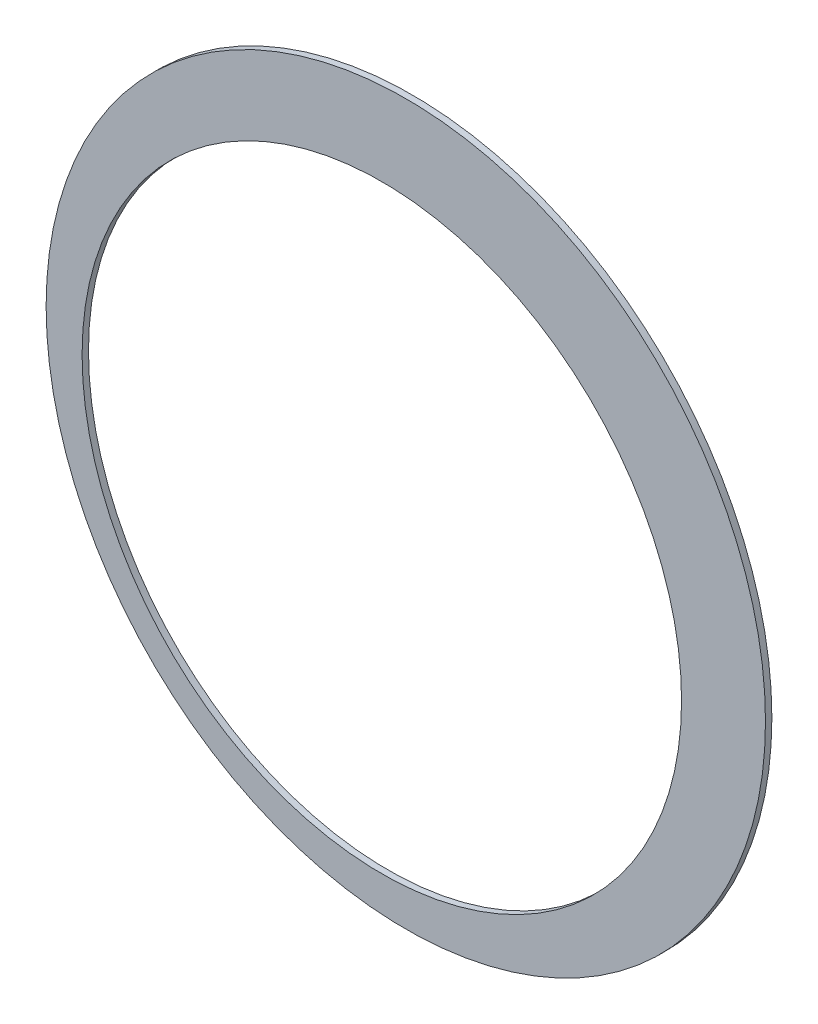
SolidWorks part; units mm, degrees
ref_plane "Front" through (0, 0, 0) normal (0, 0, 1) x (1, 0, 0)
ref_plane "Top" through (0, 0, 0) normal (0, 1, 0) x (1, 0, 0)
ref_plane "Right" through (0, 0, 0) normal (1, 0, 0) x (0, 0, -1)
sketch "Sketch1" plane through (0, 0, 0) normal (0, 0, 1) x (1, 0, 0)
  circle A0 centre (0, 0) radius 37.5
  circle A1 centre (3, 3) radius 45
  point P3 (3, 3)
  dimension "D1" = 75
  dimension "D4" = 90
  dimension "D2" = 3
  dimension "D3" = 3
sketch "Sketch2" plane through (0, 0, 0) normal (0, 0, 1) x (1, 0, 0)
  circle A0 centre (3, 3) radius 45
extrude "Base-Extrude" add sketch "Sketch2" along normal blind 0.8
sketch "Sketch3" plane through (0, 0, 0) normal (0, 0, 1) x (1, 0, 0)
  circle A0 centre (0, 0) radius 37.5
extrude "Cut-Extrude5" cut sketch "Sketch3" along normal through all
